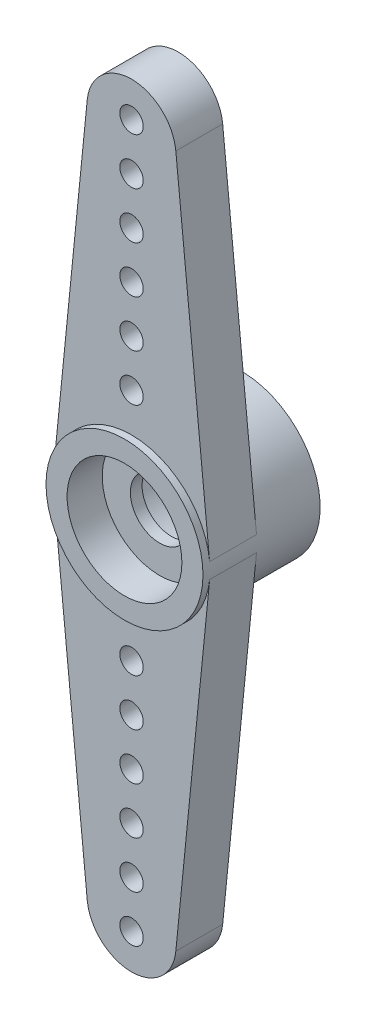
SolidWorks part; units mm, degrees
ref_plane "Спереди (Плоскость XY)" through (0, 0, 0) normal (0, 0, 1) x (1, 0, 0)
ref_plane "Сверху (Плоскость XZ)" through (0, 0, 0) normal (0, 1, 0) x (1, 0, 0)
ref_plane "Справа (Плоскость ZY)" through (0, 0, 0) normal (1, 0, 0) x (0, 0, -1)
sketch "Эскиз1" plane through (0, 0, 0) normal (0, 0, 1) x (1, 0, 0)
  line L0 (0, 0) -> (0, 50000) construction
  line L1 (0, 0) -> (-9.1549, 0) construction
  line L2 (-3.3334, 0.3327) -> (-1.8906, 14.7887)
  line L3 (3.3334, 0.3327) -> (1.8906, 14.7887)
  line L4 (-1.8906, -14.7887) -> (-3.3334, -0.3327)
  line L5 (1.8906, -14.7887) -> (3.3334, -0.3327)
  circle A0 centre (0, 0) radius 3.35 construction
  arc A1 (-1.8906, 14.7887) -> (1.8906, 14.7887) centre (0, 14.6) cw
  circle A2 centre (0, 14.6) radius 1.9 construction
  circle A3 centre (0, -14.6) radius 1.9 construction
  arc A4 (-1.8906, -14.7887) -> (1.8906, -14.7887) centre (0, -14.6) ccw
  arc A5 (3.3334, -0.3327) -> (3.3334, 0.3327) centre (0, 0) ccw
  arc A6 (-3.3334, -0.3327) -> (-3.3334, 0.3327) centre (0, 0) cw
  dimension "D1" = 6.7
  dimension "D2" = 33
  dimension "D3" = 3.8
extrude "Бобышка-Вытянуть1" add sketch "Эскиз1" along normal blind 2
sketch "Эскиз2" plane through (0, 0, 2) normal (0, 0, 1) x (1, 0, 0)
  circle A0 centre (0, 0) radius 3.35
  arc A2 (3.3334, -0.3327) -> (3.3334, 0.3327) centre (0, 0) ccw construction
  point P7 (3.35, 0)
extrude "Бобышка-Вытянуть2" add sketch "Эскиз2" along normal blind 0.3
sketch "Эскиз3" plane through (0, 0, 0) normal (0, 0, -1) x (-1, 0, 0)
  circle A0 centre (0, 0) radius 3.35
  arc A1 (3.3334, -0.3327) -> (3.3334, 0.3327) centre (0, 0) ccw construction
  point P6 (3.35, 0)
extrude "Бобышка-Вытянуть3" add sketch "Эскиз3" along normal blind 2.7
sketch "Эскиз4" plane through (0, 0, 2.3) normal (0, 0, 1) x (1, 0, 0)
  circle A0 centre (0, 0) radius 2.45
  dimension "D1" = 4.9
extrude "Вырез-Вытянуть1" cut sketch "Эскиз4" against normal blind 1.5
sketch "Эскиз5" plane through (0, 0, 0.8) normal (0, 0, 1) x (1, 0, 0)
  circle A0 centre (0, 0) radius 1.25
  dimension "D1" = 2.5
extrude "Вырез-Вытянуть2" cut sketch "Эскиз5" against normal through all
sketch "Эскиз6" plane through (0, 0, -2.7) normal (0, 0, -1) x (-1, 0, 0)
  circle A0 centre (0, 0) radius 2.45
  dimension "D1" = 4.9
extrude "Вырез-Вытянуть3" cut sketch "Эскиз6" against normal blind 3
sketch "Эскиз7" plane through (0, 0, 2) normal (0, 0, 1) x (1, 0, 0)
  line L0 (0, 0) -> (0, 50000) construction
  line L1 (0, 0) -> (50000, 0) construction
  circle A0 centre (0, 15) radius 0.5
  circle A1 centre (0, -15) radius 0.5
  circle A2 centre (0, -5) radius 0.5
  circle A3 centre (0, 5) radius 0.5
  circle A4 centre (0, -7) radius 0.5
  circle A5 centre (0, 7) radius 0.5
  circle A6 centre (0, -9) radius 0.5
  circle A7 centre (0, -11) radius 0.5
  circle A8 centre (0, 9) radius 0.5
  circle A9 centre (0, 11) radius 0.5
  circle A10 centre (0, 13) radius 0.5
  circle A11 centre (0, -13) radius 0.5
  dimension "D1" = 1
  dimension "D2" = 5
  dimension "D3" = 7
  dimension "D4" = 9
  dimension "D5" = 11
  dimension "D6" = 13
  dimension "D7" = 15
extrude "Вырез-Вытянуть4" cut sketch "Эскиз7" against normal through all
